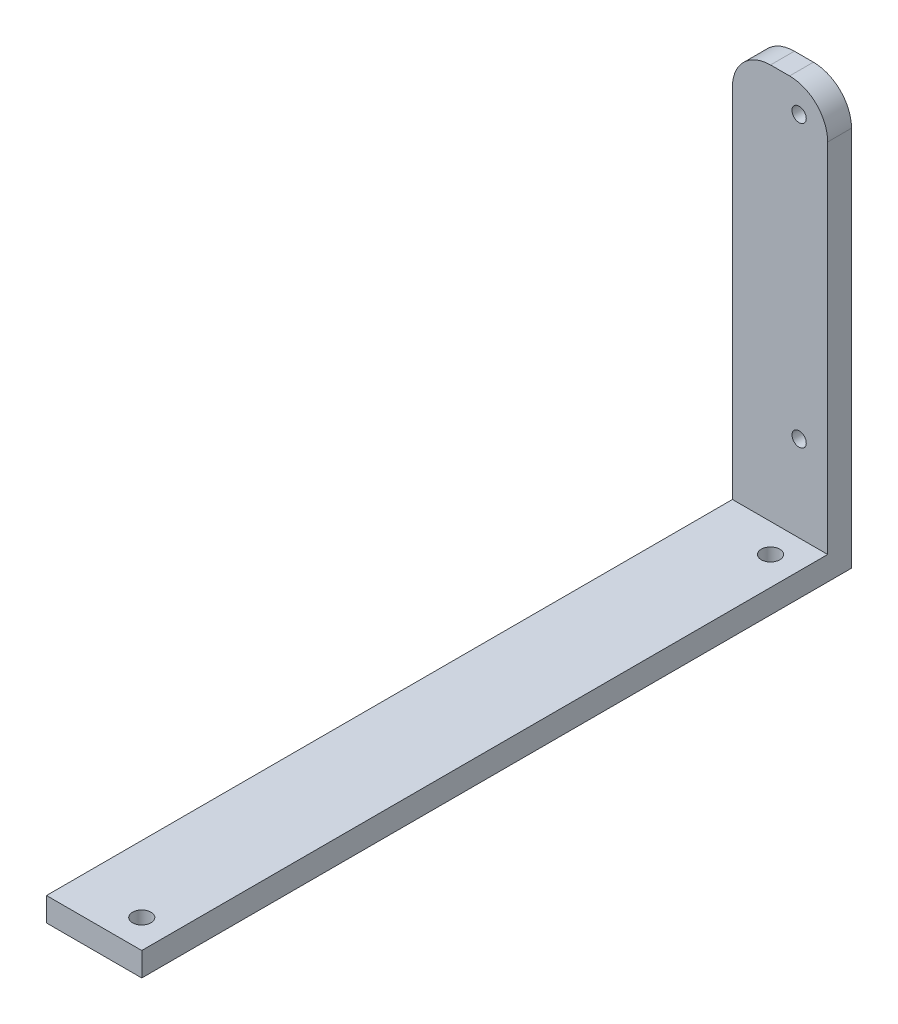
SolidWorks part; units mm, degrees
ref_plane "Front Plane" through (0, 0, 0) normal (0, 0, 1) x (1, 0, 0)
ref_plane "Top Plane" through (0, 0, 0) normal (0, 1, 0) x (1, 0, 0)
ref_plane "Right Plane" through (0, 0, 0) normal (1, 0, 0) x (0, 0, -1)
sketch "Sketch1" plane through (0, 0, 0) normal (0, 0, 1) x (1, 0, 0)
  line L1 (0, 0) -> (20, 0)
  line L2 (0, 0) -> (0, 88)
  line L3 (0, 88) -> (20, 88)
  line L4 (20, 0) -> (20, 88)
  circle A0 centre (14, 82) radius 1.5
  circle A1 centre (14, 23) radius 1.5
  dimension "D3" = 3
  dimension "D1" = 88
  dimension "D2" = 20
  dimension "D4" = 6
  dimension "D5" = 6
  dimension "D6" = 59
extrude "Boss-Extrude1" add sketch "Sketch1" along normal blind 5
sketch "Sketch2" plane through (0, 0, 5) normal (0, 0, 1) x (1, 0, 0)
  line L0 (20, 0) -> (20, 88) construction
  line L1 (0, 0) -> (20, 0)
  line L2 (0, 0) -> (0, 5)
  line L3 (0, 5) -> (20, 5)
  line L4 (20, 0) -> (20, 5)
  dimension "D1" = 5
extrude "Boss-Extrude2" add sketch "Sketch2" along normal blind 144
fillet "Fillet1" radius 8 2 edges at (20, 88, 2.5) (0, 88, 2.5)
sketch "Sketch3" plane through (0, 5, 0) normal (0, 1, 0) x (1, 0, 0)
  line L0 (20, -149) -> (0, -149) construction
  line L1 (20, -5) -> (0, -5) construction
  line L3 (20, -149) -> (20, -5) construction
  circle A0 centre (14, -143) radius 1.9394
  circle A1 centre (14, -11) radius 1.9394
  dimension "D4" = 6
  dimension "D3" = 3.8788
  dimension "D1" = 6
  dimension "D2" = 6
extrude "Cut-Extrude1" cut sketch "Sketch3" against normal through all
